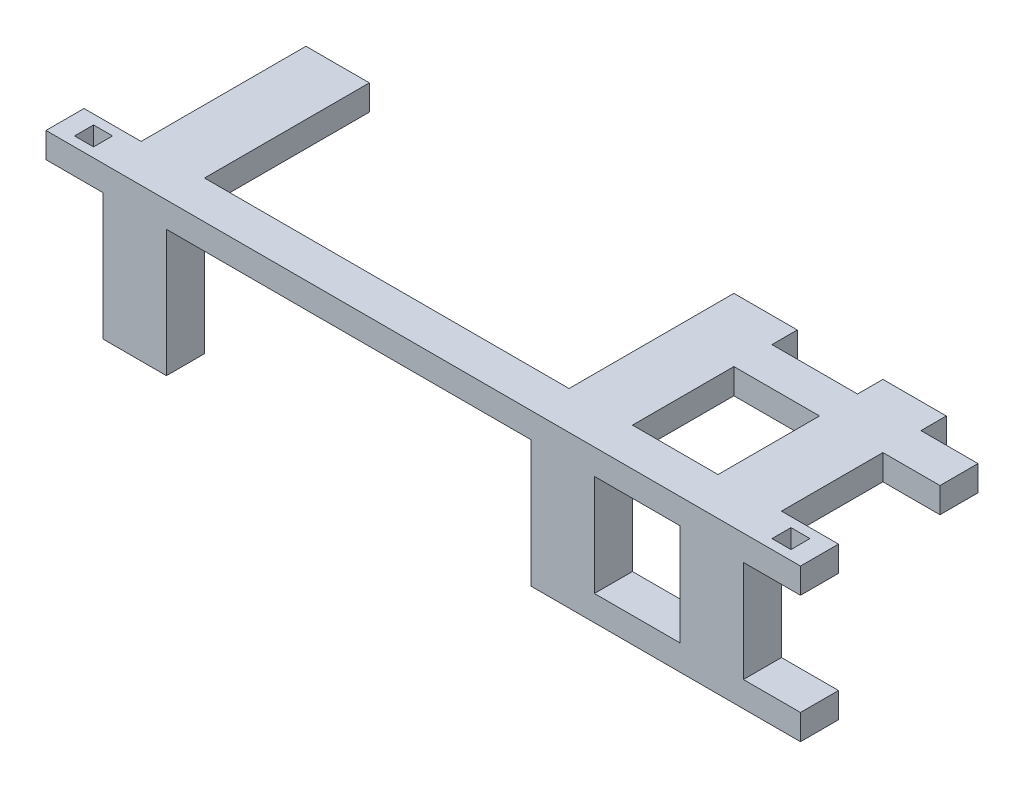
SolidWorks part; units mm, degrees
ref_plane "Front Plane" through (0, 0, 0) normal (0, 0, 1) x (1, 0, 0)
ref_plane "Top Plane" through (0, 0, 0) normal (0, 1, 0) x (1, 0, 0)
ref_plane "Right Plane" through (0, 0, 0) normal (1, 0, 0) x (0, 0, -1)
sketch "Sketch1" plane through (0, 0, 0) normal (0, 1, 0) x (1, 0, 0)
  line L1 (0, 0) -> (119, 0)
  line L2 (0, 0) -> (0, 6)
  line L3 (0, 6) -> (119, 6)
  line L4 (119, 0) -> (119, 6)
  dimension "D1" = 119
  dimension "D2" = 6
extrude "Boss-Extrude1" add sketch "Sketch1" along normal blind 4
sketch "Sketch2" plane through (0, 4, 0) normal (0, 1, 0) x (1, 0, 0)
  line L0 (119, 0) -> (119, 6) construction
  line L1 (113, 4.5) -> (116, 4.5)
  line L2 (113, 4.5) -> (113, 1.5)
  line L3 (113, 1.5) -> (116, 1.5)
  line L4 (116, 4.5) -> (116, 1.5)
  line L5 (0, 0) -> (119, 0) construction
  line L7 (0, 6) -> (0, 0) construction
  line L8 (3, 4.5) -> (6, 4.5)
  line L9 (3, 4.5) -> (3, 1.5)
  line L10 (3, 1.5) -> (6, 1.5)
  line L11 (6, 4.5) -> (6, 1.5)
  dimension "D1" = 3
  dimension "D2" = 3
  dimension "D3" = 3
  dimension "D4" = 1.5
  dimension "D5" = 3
  dimension "D6" = 3
  dimension "D7" = 3
  dimension "D8" = 1.5
extrude "Cut-Extrude1" cut sketch "Sketch2" against normal up to next
sketch "Sketch3" plane through (0, 0, -6) normal (0, 0, -1) x (-1, 0, 0)
  line L0 (-119, 4) -> (0, 4) construction
  line L1 (-110, 4) -> (-100, 4)
  line L2 (-110, 4) -> (-110, 0)
  line L3 (-110, 0) -> (-100, 0)
  line L4 (-100, 4) -> (-100, 0)
  line L5 (-119, 0) -> (0, 0) construction
  line L6 (-119, 4) -> (-119, 0) construction
  line L7 (0, 4) -> (0, 0) construction
  line L8 (-86.5, 4) -> (-76.5, 4)
  line L9 (-86.5, 4) -> (-86.5, 0)
  line L10 (-86.5, 0) -> (-76.5, 0)
  line L11 (-76.5, 4) -> (-76.5, 0)
  line L12 (-19, 4) -> (-9, 4)
  line L13 (-19, 4) -> (-19, 0)
  line L14 (-19, 0) -> (-9, 0)
  line L15 (-9, 4) -> (-9, 0)
  dimension "D1" = 9
  dimension "D2" = 10
  dimension "D3" = 13.5
  dimension "D4" = 10
  dimension "D5" = 9
  dimension "D6" = 10
extrude "Boss-Extrude2" add sketch "Sketch3" along normal blind 26
sketch "Sketch4" plane through (0, 0, 0) normal (0, -1, 0) x (1, 0, 0)
  line L0 (0, 0) -> (119, 0) construction
  line L1 (100, -6) -> (110, -6)
  line L2 (100, -6) -> (100, 0)
  line L3 (100, 0) -> (110, 0)
  line L4 (110, -6) -> (110, 0)
  line L6 (76.5, -6) -> (86.5, -6)
  line L7 (76.5, -6) -> (76.5, 0)
  line L8 (76.5, 0) -> (86.5, 0)
  line L9 (86.5, -6) -> (86.5, 0)
  line L10 (9, -6) -> (19, -6)
  line L11 (9, -6) -> (9, 0)
  line L12 (9, 0) -> (19, 0)
  line L13 (19, -6) -> (19, 0)
  dimension "D1" = 10
  dimension "D2" = 10
  dimension "D3" = 10
extrude "Boss-Extrude3" add sketch "Sketch4" along normal blind 20
sketch "Sketch5" plane through (76.5, 0, 0) normal (-1, 0, 0) x (0, 0, 1)
  line L0 (-32, 4) -> (-6, 4) construction
  line L1 (-28, 4) -> (-22, 4)
  line L2 (-28, 4) -> (-28, 0)
  line L3 (-28, 0) -> (-22, 0)
  line L4 (-22, 4) -> (-22, 0)
  line L5 (-32, 0) -> (-6, 0) construction
  line L6 (-32, 0) -> (-32, 4) construction
  line L7 (0, -20) -> (0, 0) construction
  line L8 (-6, -20) -> (0, -20)
  line L9 (-6, -20) -> (-6, -16)
  line L10 (-6, -16) -> (0, -16)
  line L11 (0, -20) -> (0, -16)
  dimension "D1" = 4
  dimension "D2" = 6
  dimension "D3" = 4
extrude "Boss-Extrude4" add sketch "Sketch5" against normal blind 42.5
